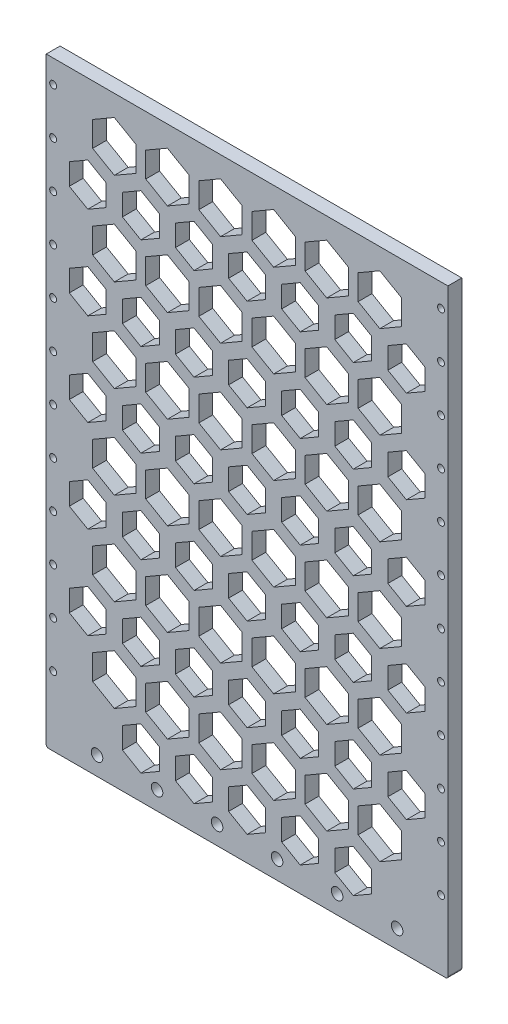
SolidWorks part; units mm, degrees
material "6061 Alloy"
ref_plane "前视基准面" through (0, 0, 0) normal (0, 0, 1) x (1, 0, 0)
ref_plane "上视基准面" through (0, 0, 0) normal (0, 1, 0) x (1, 0, 0)
ref_plane "右视基准面" through (0, 0, 0) normal (1, 0, 0) x (0, 0, -1)
sketch "Sketch1" plane through (0, 0, 0) normal (0, 0, 1) x (1, 0, 0)
  line L1 (-87, 90) -> (87, 90)
  line L2 (-87, 90) -> (-87, -150)
  line L3 (-87, -150) -> (87, -150)
  line L4 (87, 90) -> (87, -150)
  line L5 (-87, 90) -> (87, -150) construction
  line L6 (-87, -150) -> (87, 90) construction
  point P0 (0, -30)
  dimension "D1" = 174
  dimension "D2" = 240
extrude "Boss-Extrude1" add sketch "Sketch1" along normal blind 6
sketch "Sketch3" plane through (0, 0, 6) normal (0, 0, 1) x (1, 0, 0)
  line L6 (-77, -134) -> (77, -134) construction
  line L7 (-77, -134) -> (-77, -150) construction
  line L8 (-77, -150) -> (77, -150) construction
  line L9 (77, -134) -> (77, -150) construction
  line L10 (-77, -134) -> (77, -150) construction
  line L11 (-77, -150) -> (77, -134) construction
  circle A0 centre (-65, -142) radius 2.5
  circle A1 centre (-39, -142) radius 2.5
  circle A2 centre (-13, -142) radius 2.5
  circle A3 centre (13, -142) radius 2.5
  circle A4 centre (39, -142) radius 2.5
  circle A5 centre (65, -142) radius 2.5
  point P0 (0, -142)
  dimension "D1" = 12
  dimension "D2" = 6
extrude "Cut-Extrude1" cut sketch "Sketch3" against normal blind 6 contours A0 | A1 | A2 | A3 | A4 | A5
sketch "Sketch4" plane through (0, 90, 0) normal (0, 1, 0) x (1, 0, 0)
  line L4 (87, 0) -> (-87, 0)
  line L5 (-87, 0) -> (-87, -6)
  line L6 (-87, -6) -> (87, -6)
  line L7 (87, -6) -> (87, 0)
  line L8 (87, 0) -> (-87, 0)
  line L9 (-87, 0) -> (-87, -6)
  line L10 (-87, -6) -> (87, -6)
  line L11 (87, -6) -> (87, 0)
  dimension "D1" = 0
extrude "Boss-Extrude2" add sketch "Sketch4" along normal blind 20
sketch "Sketch6" plane through (0, 0, 6) normal (0, 0, 1) x (1, 0, 0)
  line L0 (-87, 110) -> (87, 110) construction
  line L2 (-87, 110) -> (-87, -150) construction
  line L3 (87, -150) -> (87, 110) construction
  circle A0 centre (-84, 100) radius 1.5
  circle A1 centre (-84, 80) radius 1.5
  circle A2 centre (-84, 60) radius 1.5
  circle A3 centre (-84, 40) radius 1.5
  circle A4 centre (-84, 20) radius 1.5
  circle A5 centre (-84, 0) radius 1.5
  circle A6 centre (-84, -20) radius 1.5
  circle A7 centre (-84, -40) radius 1.5
  circle A8 centre (-84, -60) radius 1.5
  circle A9 centre (-84, -80) radius 1.5
  circle A10 centre (-84, -100) radius 1.5
  circle A11 centre (-84, -120) radius 1.5
  circle A15 centre (84, 100) radius 1.5
  circle A16 centre (84, 80) radius 1.5
  circle A17 centre (84, 60) radius 1.5
  circle A18 centre (84, 40) radius 1.5
  circle A19 centre (84, 20) radius 1.5
  circle A20 centre (84, 0) radius 1.5
  circle A21 centre (84, -20) radius 1.5
  circle A22 centre (84, -40) radius 1.5
  circle A23 centre (84, -60) radius 1.5
  circle A24 centre (84, -80) radius 1.5
  circle A25 centre (84, -100) radius 1.5
  circle A26 centre (84, -120) radius 1.5
  circle A30 centre (-84, -160) radius 1.5 [skipped]
  circle A31 centre (-84, -180) radius 1.5 [skipped]
  circle A32 centre (84, -160) radius 1.5 [skipped]
  circle A33 centre (84, -180) radius 1.5 [skipped]
  circle A34 centre (-84, -140) radius 1.5 [skipped]
  circle A35 centre (84, -140) radius 1.5 [skipped]
  dimension "D3" = 15
  dimension "D5" = 3
  dimension "D1" = 10
  dimension "D2" = 3
  dimension "D4" = 3
  dimension "D6" = 10
  dimension "D7" = 15
extrude "Cut-Extrude2" cut sketch "Sketch6" against normal blind 10
sketch "Sketch7" plane through (0, 0, 6) normal (0, 0, 1) x (1, 0, 0)
  line L80 (-46, 60.7624) -> (-38, 65.3812)
  line L81 (-38, 65.3812) -> (-38, 74.6188)
  line L82 (-38, 74.6188) -> (-46, 79.2376)
  line L83 (-46, 79.2376) -> (-54, 74.6188)
  line L84 (-54, 74.6188) -> (-54, 65.3812)
  line L85 (-54, 65.3812) -> (-46, 60.7624)
  line L86 (-23, 60.7624) -> (-15, 65.3812)
  line L87 (-15, 65.3812) -> (-15, 74.6188)
  line L88 (-15, 74.6188) -> (-23, 79.2376)
  line L89 (-23, 79.2376) -> (-31, 74.6188)
  line L90 (-31, 74.6188) -> (-31, 65.3812)
  line L91 (-31, 65.3812) -> (-23, 60.7624)
  line L92 (0, 60.7624) -> (8, 65.3812)
  line L93 (8, 65.3812) -> (8, 74.6188)
  line L94 (8, 74.6188) -> (0, 79.2376)
  line L95 (0, 79.2376) -> (-8, 74.6188)
  line L96 (-8, 74.6188) -> (-8, 65.3812)
  line L97 (-8, 65.3812) -> (0, 60.7624)
  line L98 (23, 60.7624) -> (31, 65.3812)
  line L99 (31, 65.3812) -> (31, 74.6188)
  line L100 (31, 74.6188) -> (23, 79.2376)
  line L101 (23, 79.2376) -> (15, 74.6188)
  line L102 (15, 74.6188) -> (15, 65.3812)
  line L103 (15, 65.3812) -> (23, 60.7624)
  line L104 (46, 60.7624) -> (54, 65.3812)
  line L105 (54, 65.3812) -> (54, 74.6188)
  line L106 (54, 74.6188) -> (46, 79.2376)
  line L107 (46, 79.2376) -> (38, 74.6188)
  line L108 (38, 74.6188) -> (38, 65.3812)
  line L109 (38, 65.3812) -> (46, 60.7624)
  line L110 (69, 60.7624) -> (77, 65.3812)
  line L111 (77, 65.3812) -> (77, 74.6188)
  line L112 (77, 74.6188) -> (69, 79.2376)
  line L113 (69, 79.2376) -> (61, 74.6188)
  line L114 (61, 74.6188) -> (61, 65.3812)
  line L115 (61, 65.3812) -> (69, 60.7624)
  line L116 (-46, 20.7624) -> (-38, 25.3812)
  line L117 (-38, 25.3812) -> (-38, 34.6188)
  line L118 (-38, 34.6188) -> (-46, 39.2376)
  line L119 (-46, 39.2376) -> (-54, 34.6188)
  line L120 (-54, 34.6188) -> (-54, 25.3812)
  line L121 (-54, 25.3812) -> (-46, 20.7624)
  line L122 (-23, 20.7624) -> (-15, 25.3812)
  line L123 (-15, 25.3812) -> (-15, 34.6188)
  line L124 (-15, 34.6188) -> (-23, 39.2376)
  line L125 (-23, 39.2376) -> (-31, 34.6188)
  line L126 (-31, 34.6188) -> (-31, 25.3812)
  line L127 (-31, 25.3812) -> (-23, 20.7624)
  line L128 (0, 20.7624) -> (8, 25.3812)
  line L129 (8, 25.3812) -> (8, 34.6188)
  line L130 (8, 34.6188) -> (0, 39.2376)
  line L131 (0, 39.2376) -> (-8, 34.6188)
  line L132 (-8, 34.6188) -> (-8, 25.3812)
  line L133 (-8, 25.3812) -> (0, 20.7624)
  line L134 (23, 20.7624) -> (31, 25.3812)
  line L135 (31, 25.3812) -> (31, 34.6188)
  line L136 (31, 34.6188) -> (23, 39.2376)
  line L137 (23, 39.2376) -> (15, 34.6188)
  line L138 (15, 34.6188) -> (15, 25.3812)
  line L139 (15, 25.3812) -> (23, 20.7624)
  line L140 (46, 20.7624) -> (54, 25.3812)
  line L141 (54, 25.3812) -> (54, 34.6188)
  line L142 (54, 34.6188) -> (46, 39.2376)
  line L143 (46, 39.2376) -> (38, 34.6188)
  line L144 (38, 34.6188) -> (38, 25.3812)
  line L145 (38, 25.3812) -> (46, 20.7624)
  line L146 (69, 20.7624) -> (77, 25.3812)
  line L147 (77, 25.3812) -> (77, 34.6188)
  line L148 (77, 34.6188) -> (69, 39.2376)
  line L149 (69, 39.2376) -> (61, 34.6188)
  line L150 (61, 34.6188) -> (61, 25.3812)
  line L151 (61, 25.3812) -> (69, 20.7624)
  line L152 (-46, -19.2376) -> (-38, -14.6188)
  line L153 (-38, -14.6188) -> (-38, -5.3812)
  line L154 (-38, -5.3812) -> (-46, -0.7624)
  line L155 (-46, -0.7624) -> (-54, -5.3812)
  line L156 (-54, -5.3812) -> (-54, -14.6188)
  line L157 (-54, -14.6188) -> (-46, -19.2376)
  line L158 (-23, -19.2376) -> (-15, -14.6188)
  line L159 (-15, -14.6188) -> (-15, -5.3812)
  line L160 (-15, -5.3812) -> (-23, -0.7624)
  line L161 (-23, -0.7624) -> (-31, -5.3812)
  line L162 (-31, -5.3812) -> (-31, -14.6188)
  line L163 (-31, -14.6188) -> (-23, -19.2376)
  line L164 (0, -19.2376) -> (8, -14.6188)
  line L165 (8, -14.6188) -> (8, -5.3812)
  line L166 (8, -5.3812) -> (0, -0.7624)
  line L167 (0, -0.7624) -> (-8, -5.3812)
  line L168 (-8, -5.3812) -> (-8, -14.6188)
  line L169 (-8, -14.6188) -> (0, -19.2376)
  line L170 (23, -19.2376) -> (31, -14.6188)
  line L171 (31, -14.6188) -> (31, -5.3812)
  line L172 (31, -5.3812) -> (23, -0.7624)
  line L173 (23, -0.7624) -> (15, -5.3812)
  line L174 (15, -5.3812) -> (15, -14.6188)
  line L175 (15, -14.6188) -> (23, -19.2376)
  line L176 (46, -19.2376) -> (54, -14.6188)
  line L177 (54, -14.6188) -> (54, -5.3812)
  line L178 (54, -5.3812) -> (46, -0.7624)
  line L179 (46, -0.7624) -> (38, -5.3812)
  line L180 (38, -5.3812) -> (38, -14.6188)
  line L181 (38, -14.6188) -> (46, -19.2376)
  line L182 (69, -19.2376) -> (77, -14.6188)
  line L183 (77, -14.6188) -> (77, -5.3812)
  line L184 (77, -5.3812) -> (69, -0.7624)
  line L185 (69, -0.7624) -> (61, -5.3812)
  line L186 (61, -5.3812) -> (61, -14.6188)
  line L187 (61, -14.6188) -> (69, -19.2376)
  line L188 (-46, -59.2376) -> (-38, -54.6188)
  line L189 (-38, -54.6188) -> (-38, -45.3812)
  line L190 (-38, -45.3812) -> (-46, -40.7624)
  line L191 (-46, -40.7624) -> (-54, -45.3812)
  line L192 (-54, -45.3812) -> (-54, -54.6188)
  line L193 (-54, -54.6188) -> (-46, -59.2376)
  line L194 (-23, -59.2376) -> (-15, -54.6188)
  line L195 (-15, -54.6188) -> (-15, -45.3812)
  line L196 (-15, -45.3812) -> (-23, -40.7624)
  line L197 (-23, -40.7624) -> (-31, -45.3812)
  line L198 (-31, -45.3812) -> (-31, -54.6188)
  line L199 (-31, -54.6188) -> (-23, -59.2376)
  line L200 (0, -59.2376) -> (8, -54.6188)
  line L201 (8, -54.6188) -> (8, -45.3812)
  line L202 (8, -45.3812) -> (0, -40.7624)
  line L203 (0, -40.7624) -> (-8, -45.3812)
  line L204 (-8, -45.3812) -> (-8, -54.6188)
  line L205 (-8, -54.6188) -> (0, -59.2376)
  line L206 (23, -59.2376) -> (31, -54.6188)
  line L207 (31, -54.6188) -> (31, -45.3812)
  line L208 (31, -45.3812) -> (23, -40.7624)
  line L209 (23, -40.7624) -> (15, -45.3812)
  line L210 (15, -45.3812) -> (15, -54.6188)
  line L211 (15, -54.6188) -> (23, -59.2376)
  line L212 (46, -59.2376) -> (54, -54.6188)
  line L213 (54, -54.6188) -> (54, -45.3812)
  line L214 (54, -45.3812) -> (46, -40.7624)
  line L215 (46, -40.7624) -> (38, -45.3812)
  line L216 (38, -45.3812) -> (38, -54.6188)
  line L217 (38, -54.6188) -> (46, -59.2376)
  line L218 (69, -59.2376) -> (77, -54.6188)
  line L219 (77, -54.6188) -> (77, -45.3812)
  line L220 (77, -45.3812) -> (69, -40.7624)
  line L221 (69, -40.7624) -> (61, -45.3812)
  line L222 (61, -45.3812) -> (61, -54.6188)
  line L223 (61, -54.6188) -> (69, -59.2376)
  line L224 (-46, -99.2376) -> (-38, -94.6188)
  line L225 (-38, -94.6188) -> (-38, -85.3812)
  line L226 (-38, -85.3812) -> (-46, -80.7624)
  line L227 (-46, -80.7624) -> (-54, -85.3812)
  line L228 (-54, -85.3812) -> (-54, -94.6188)
  line L229 (-54, -94.6188) -> (-46, -99.2376)
  line L230 (-23, -99.2376) -> (-15, -94.6188)
  line L231 (-15, -94.6188) -> (-15, -85.3812)
  line L232 (-15, -85.3812) -> (-23, -80.7624)
  line L233 (-23, -80.7624) -> (-31, -85.3812)
  line L234 (-31, -85.3812) -> (-31, -94.6188)
  line L235 (-31, -94.6188) -> (-23, -99.2376)
  line L236 (0, -99.2376) -> (8, -94.6188)
  line L237 (8, -94.6188) -> (8, -85.3812)
  line L238 (8, -85.3812) -> (0, -80.7624)
  line L239 (0, -80.7624) -> (-8, -85.3812)
  line L240 (-8, -85.3812) -> (-8, -94.6188)
  line L241 (-8, -94.6188) -> (0, -99.2376)
  line L242 (23, -99.2376) -> (31, -94.6188)
  line L243 (31, -94.6188) -> (31, -85.3812)
  line L244 (31, -85.3812) -> (23, -80.7624)
  line L245 (23, -80.7624) -> (15, -85.3812)
  line L246 (15, -85.3812) -> (15, -94.6188)
  line L247 (15, -94.6188) -> (23, -99.2376)
  line L248 (46, -99.2376) -> (54, -94.6188)
  line L249 (54, -94.6188) -> (54, -85.3812)
  line L250 (54, -85.3812) -> (46, -80.7624)
  line L251 (46, -80.7624) -> (38, -85.3812)
  line L252 (38, -85.3812) -> (38, -94.6188)
  line L253 (38, -94.6188) -> (46, -99.2376)
  line L254 (69, -99.2376) -> (77, -94.6188)
  line L255 (77, -94.6188) -> (77, -85.3812)
  line L256 (77, -85.3812) -> (69, -80.7624)
  line L257 (69, -80.7624) -> (61, -85.3812)
  line L258 (61, -85.3812) -> (61, -94.6188)
  line L259 (61, -94.6188) -> (69, -99.2376)
  line L260 (-46, -139.2376) -> (-38, -134.6188)
  line L261 (-38, -134.6188) -> (-38, -125.3812)
  line L262 (-38, -125.3812) -> (-46, -120.7624)
  line L263 (-46, -120.7624) -> (-54, -125.3812)
  line L264 (-54, -125.3812) -> (-54, -134.6188)
  line L265 (-54, -134.6188) -> (-46, -139.2376)
  line L266 (-23, -139.2376) -> (-15, -134.6188)
  line L267 (-15, -134.6188) -> (-15, -125.3812)
  line L268 (-15, -125.3812) -> (-23, -120.7624)
  line L269 (-23, -120.7624) -> (-31, -125.3812)
  line L270 (-31, -125.3812) -> (-31, -134.6188)
  line L271 (-31, -134.6188) -> (-23, -139.2376)
  line L272 (0, -139.2376) -> (8, -134.6188)
  line L273 (8, -134.6188) -> (8, -125.3812)
  line L274 (8, -125.3812) -> (0, -120.7624)
  line L275 (0, -120.7624) -> (-8, -125.3812)
  line L276 (-8, -125.3812) -> (-8, -134.6188)
  line L277 (-8, -134.6188) -> (0, -139.2376)
  line L278 (23, -139.2376) -> (31, -134.6188)
  line L279 (31, -134.6188) -> (31, -125.3812)
  line L280 (31, -125.3812) -> (23, -120.7624)
  line L281 (23, -120.7624) -> (15, -125.3812)
  line L282 (15, -125.3812) -> (15, -134.6188)
  line L283 (15, -134.6188) -> (23, -139.2376)
  line L284 (46, -139.2376) -> (54, -134.6188)
  line L285 (54, -134.6188) -> (54, -125.3812)
  line L286 (54, -125.3812) -> (46, -120.7624)
  line L287 (46, -120.7624) -> (38, -125.3812)
  line L288 (38, -125.3812) -> (38, -134.6188)
  line L289 (38, -134.6188) -> (46, -139.2376)
  line L302 (-69, 60.7624) -> (-61, 65.3812)
  line L303 (-61, 65.3812) -> (-61, 74.6188)
  line L304 (-61, 74.6188) -> (-69, 79.2376)
  line L305 (-69, 79.2376) -> (-77, 74.6188)
  line L306 (-77, 74.6188) -> (-77, 65.3812)
  line L307 (-77, 65.3812) -> (-69, 60.7624)
  line L308 (-69, 20.7624) -> (-61, 25.3812)
  line L309 (-61, 25.3812) -> (-61, 34.6188)
  line L310 (-61, 34.6188) -> (-69, 39.2376)
  line L311 (-69, 39.2376) -> (-77, 34.6188)
  line L312 (-77, 34.6188) -> (-77, 25.3812)
  line L313 (-77, 25.3812) -> (-69, 20.7624)
  line L314 (-69, -19.2376) -> (-61, -14.6188)
  line L315 (-61, -14.6188) -> (-61, -5.3812)
  line L316 (-61, -5.3812) -> (-69, -0.7624)
  line L317 (-69, -0.7624) -> (-77, -5.3812)
  line L318 (-77, -5.3812) -> (-77, -14.6188)
  line L319 (-77, -14.6188) -> (-69, -19.2376)
  line L320 (-69, -59.2376) -> (-61, -54.6188)
  line L321 (-61, -54.6188) -> (-61, -45.3812)
  line L322 (-61, -45.3812) -> (-69, -40.7624)
  line L323 (-69, -40.7624) -> (-77, -45.3812)
  line L324 (-77, -45.3812) -> (-77, -54.6188)
  line L325 (-77, -54.6188) -> (-69, -59.2376)
  line L326 (-69, -99.2376) -> (-61, -94.6188)
  line L327 (-61, -94.6188) -> (-61, -85.3812)
  line L328 (-61, -85.3812) -> (-69, -80.7624)
  line L329 (-69, -80.7624) -> (-77, -85.3812)
  line L330 (-77, -85.3812) -> (-77, -94.6188)
  line L331 (-77, -94.6188) -> (-69, -99.2376)
  line L376 (-34.5, 79.2376) -> (-25.109, 84.6595)
  line L377 (-25.109, 84.6595) -> (-25.109, 95.5033)
  line L378 (-25.109, 95.5033) -> (-34.5, 100.9252)
  line L379 (-34.5, 100.9252) -> (-43.891, 95.5033)
  line L380 (-43.891, 95.5033) -> (-43.891, 84.6595)
  line L381 (-43.891, 84.6595) -> (-34.5, 79.2376)
  line L382 (-11.5, 79.2376) -> (-2.109, 84.6595)
  line L383 (-2.109, 84.6595) -> (-2.109, 95.5033)
  line L384 (-2.109, 95.5033) -> (-11.5, 100.9252)
  line L385 (-11.5, 100.9252) -> (-20.891, 95.5033)
  line L386 (-20.891, 95.5033) -> (-20.891, 84.6595)
  line L387 (-20.891, 84.6595) -> (-11.5, 79.2376)
  line L388 (11.5, 79.2376) -> (20.891, 84.6595)
  line L389 (20.891, 84.6595) -> (20.891, 95.5033)
  line L390 (20.891, 95.5033) -> (11.5, 100.9252)
  line L391 (11.5, 100.9252) -> (2.109, 95.5033)
  line L392 (2.109, 95.5033) -> (2.109, 84.6595)
  line L393 (2.109, 84.6595) -> (11.5, 79.2376)
  line L394 (34.5, 79.2376) -> (43.891, 84.6595)
  line L395 (43.891, 84.6595) -> (43.891, 95.5033)
  line L396 (43.891, 95.5033) -> (34.5, 100.9252)
  line L397 (34.5, 100.9252) -> (25.109, 95.5033)
  line L398 (25.109, 95.5033) -> (25.109, 84.6595)
  line L399 (25.109, 84.6595) -> (34.5, 79.2376)
  line L400 (57.5, 79.2376) -> (66.891, 84.6595)
  line L401 (66.891, 84.6595) -> (66.891, 95.5033)
  line L402 (66.891, 95.5033) -> (57.5, 100.9252)
  line L403 (57.5, 100.9252) -> (48.109, 95.5033)
  line L404 (48.109, 95.5033) -> (48.109, 84.6595)
  line L405 (48.109, 84.6595) -> (57.5, 79.2376)
  line L406 (-34.5, 39.2376) -> (-25.109, 44.6595)
  line L407 (-25.109, 44.6595) -> (-25.109, 55.5033)
  line L408 (-25.109, 55.5033) -> (-34.5, 60.9252)
  line L409 (-34.5, 60.9252) -> (-43.891, 55.5033)
  line L410 (-43.891, 55.5033) -> (-43.891, 44.6595)
  line L411 (-43.891, 44.6595) -> (-34.5, 39.2376)
  line L412 (-11.5, 39.2376) -> (-2.109, 44.6595)
  line L413 (-2.109, 44.6595) -> (-2.109, 55.5033)
  line L414 (-2.109, 55.5033) -> (-11.5, 60.9252)
  line L415 (-11.5, 60.9252) -> (-20.891, 55.5033)
  line L416 (-20.891, 55.5033) -> (-20.891, 44.6595)
  line L417 (-20.891, 44.6595) -> (-11.5, 39.2376)
  line L418 (11.5, 39.2376) -> (20.891, 44.6595)
  line L419 (20.891, 44.6595) -> (20.891, 55.5033)
  line L420 (20.891, 55.5033) -> (11.5, 60.9252)
  line L421 (11.5, 60.9252) -> (2.109, 55.5033)
  line L422 (2.109, 55.5033) -> (2.109, 44.6595)
  line L423 (2.109, 44.6595) -> (11.5, 39.2376)
  line L424 (34.5, 39.2376) -> (43.891, 44.6595)
  line L425 (43.891, 44.6595) -> (43.891, 55.5033)
  line L426 (43.891, 55.5033) -> (34.5, 60.9252)
  line L427 (34.5, 60.9252) -> (25.109, 55.5033)
  line L428 (25.109, 55.5033) -> (25.109, 44.6595)
  line L429 (25.109, 44.6595) -> (34.5, 39.2376)
  line L430 (57.5, 39.2376) -> (66.891, 44.6595)
  line L431 (66.891, 44.6595) -> (66.891, 55.5033)
  line L432 (66.891, 55.5033) -> (57.5, 60.9252)
  line L433 (57.5, 60.9252) -> (48.109, 55.5033)
  line L434 (48.109, 55.5033) -> (48.109, 44.6595)
  line L435 (48.109, 44.6595) -> (57.5, 39.2376)
  line L436 (-34.5, -0.7624) -> (-25.109, 4.6595)
  line L437 (-25.109, 4.6595) -> (-25.109, 15.5033)
  line L438 (-25.109, 15.5033) -> (-34.5, 20.9252)
  line L439 (-34.5, 20.9252) -> (-43.891, 15.5033)
  line L440 (-43.891, 15.5033) -> (-43.891, 4.6595)
  line L441 (-43.891, 4.6595) -> (-34.5, -0.7624)
  line L442 (-11.5, -0.7624) -> (-2.109, 4.6595)
  line L443 (-2.109, 4.6595) -> (-2.109, 15.5033)
  line L444 (-2.109, 15.5033) -> (-11.5, 20.9252)
  line L445 (-11.5, 20.9252) -> (-20.891, 15.5033)
  line L446 (-20.891, 15.5033) -> (-20.891, 4.6595)
  line L447 (-20.891, 4.6595) -> (-11.5, -0.7624)
  line L448 (11.5, -0.7624) -> (20.891, 4.6595)
  line L449 (20.891, 4.6595) -> (20.891, 15.5033)
  line L450 (20.891, 15.5033) -> (11.5, 20.9252)
  line L451 (11.5, 20.9252) -> (2.109, 15.5033)
  line L452 (2.109, 15.5033) -> (2.109, 4.6595)
  line L453 (2.109, 4.6595) -> (11.5, -0.7624)
  line L454 (34.5, -0.7624) -> (43.891, 4.6595)
  line L455 (43.891, 4.6595) -> (43.891, 15.5033)
  line L456 (43.891, 15.5033) -> (34.5, 20.9252)
  line L457 (34.5, 20.9252) -> (25.109, 15.5033)
  line L458 (25.109, 15.5033) -> (25.109, 4.6595)
  line L459 (25.109, 4.6595) -> (34.5, -0.7624)
  line L460 (57.5, -0.7624) -> (66.891, 4.6595)
  line L461 (66.891, 4.6595) -> (66.891, 15.5033)
  line L462 (66.891, 15.5033) -> (57.5, 20.9252)
  line L463 (57.5, 20.9252) -> (48.109, 15.5033)
  line L464 (48.109, 15.5033) -> (48.109, 4.6595)
  line L465 (48.109, 4.6595) -> (57.5, -0.7624)
  line L466 (-34.5, -40.7624) -> (-25.109, -35.3405)
  line L467 (-25.109, -35.3405) -> (-25.109, -24.4967)
  line L468 (-25.109, -24.4967) -> (-34.5, -19.0748)
  line L469 (-34.5, -19.0748) -> (-43.891, -24.4967)
  line L470 (-43.891, -24.4967) -> (-43.891, -35.3405)
  line L471 (-43.891, -35.3405) -> (-34.5, -40.7624)
  line L472 (-11.5, -40.7624) -> (-2.109, -35.3405)
  line L473 (-2.109, -35.3405) -> (-2.109, -24.4967)
  line L474 (-2.109, -24.4967) -> (-11.5, -19.0748)
  line L475 (-11.5, -19.0748) -> (-20.891, -24.4967)
  line L476 (-20.891, -24.4967) -> (-20.891, -35.3405)
  line L477 (-20.891, -35.3405) -> (-11.5, -40.7624)
  line L478 (11.5, -40.7624) -> (20.891, -35.3405)
  line L479 (20.891, -35.3405) -> (20.891, -24.4967)
  line L480 (20.891, -24.4967) -> (11.5, -19.0748)
  line L481 (11.5, -19.0748) -> (2.109, -24.4967)
  line L482 (2.109, -24.4967) -> (2.109, -35.3405)
  line L483 (2.109, -35.3405) -> (11.5, -40.7624)
  line L484 (34.5, -40.7624) -> (43.891, -35.3405)
  line L485 (43.891, -35.3405) -> (43.891, -24.4967)
  line L486 (43.891, -24.4967) -> (34.5, -19.0748)
  line L487 (34.5, -19.0748) -> (25.109, -24.4967)
  line L488 (25.109, -24.4967) -> (25.109, -35.3405)
  line L489 (25.109, -35.3405) -> (34.5, -40.7624)
  line L490 (57.5, -40.7624) -> (66.891, -35.3405)
  line L491 (66.891, -35.3405) -> (66.891, -24.4967)
  line L492 (66.891, -24.4967) -> (57.5, -19.0748)
  line L493 (57.5, -19.0748) -> (48.109, -24.4967)
  line L494 (48.109, -24.4967) -> (48.109, -35.3405)
  line L495 (48.109, -35.3405) -> (57.5, -40.7624)
  line L496 (-34.5, -80.7624) -> (-25.109, -75.3405)
  line L497 (-25.109, -75.3405) -> (-25.109, -64.4967)
  line L498 (-25.109, -64.4967) -> (-34.5, -59.0748)
  line L499 (-34.5, -59.0748) -> (-43.891, -64.4967)
  line L500 (-43.891, -64.4967) -> (-43.891, -75.3405)
  line L501 (-43.891, -75.3405) -> (-34.5, -80.7624)
  line L502 (-11.5, -80.7624) -> (-2.109, -75.3405)
  line L503 (-2.109, -75.3405) -> (-2.109, -64.4967)
  line L504 (-2.109, -64.4967) -> (-11.5, -59.0748)
  line L505 (-11.5, -59.0748) -> (-20.891, -64.4967)
  line L506 (-20.891, -64.4967) -> (-20.891, -75.3405)
  line L507 (-20.891, -75.3405) -> (-11.5, -80.7624)
  line L508 (11.5, -80.7624) -> (20.891, -75.3405)
  line L509 (20.891, -75.3405) -> (20.891, -64.4967)
  line L510 (20.891, -64.4967) -> (11.5, -59.0748)
  line L511 (11.5, -59.0748) -> (2.109, -64.4967)
  line L512 (2.109, -64.4967) -> (2.109, -75.3405)
  line L513 (2.109, -75.3405) -> (11.5, -80.7624)
  line L514 (34.5, -80.7624) -> (43.891, -75.3405)
  line L515 (43.891, -75.3405) -> (43.891, -64.4967)
  line L516 (43.891, -64.4967) -> (34.5, -59.0748)
  line L517 (34.5, -59.0748) -> (25.109, -64.4967)
  line L518 (25.109, -64.4967) -> (25.109, -75.3405)
  line L519 (25.109, -75.3405) -> (34.5, -80.7624)
  line L520 (57.5, -80.7624) -> (66.891, -75.3405)
  line L521 (66.891, -75.3405) -> (66.891, -64.4967)
  line L522 (66.891, -64.4967) -> (57.5, -59.0748)
  line L523 (57.5, -59.0748) -> (48.109, -64.4967)
  line L524 (48.109, -64.4967) -> (48.109, -75.3405)
  line L525 (48.109, -75.3405) -> (57.5, -80.7624)
  line L526 (-34.5, -120.7624) -> (-25.109, -115.3405)
  line L527 (-25.109, -115.3405) -> (-25.109, -104.4967)
  line L528 (-25.109, -104.4967) -> (-34.5, -99.0748)
  line L529 (-34.5, -99.0748) -> (-43.891, -104.4967)
  line L530 (-43.891, -104.4967) -> (-43.891, -115.3405)
  line L531 (-43.891, -115.3405) -> (-34.5, -120.7624)
  line L532 (-11.5, -120.7624) -> (-2.109, -115.3405)
  line L533 (-2.109, -115.3405) -> (-2.109, -104.4967)
  line L534 (-2.109, -104.4967) -> (-11.5, -99.0748)
  line L535 (-11.5, -99.0748) -> (-20.891, -104.4967)
  line L536 (-20.891, -104.4967) -> (-20.891, -115.3405)
  line L537 (-20.891, -115.3405) -> (-11.5, -120.7624)
  line L538 (11.5, -120.7624) -> (20.891, -115.3405)
  line L539 (20.891, -115.3405) -> (20.891, -104.4967)
  line L540 (20.891, -104.4967) -> (11.5, -99.0748)
  line L541 (11.5, -99.0748) -> (2.109, -104.4967)
  line L542 (2.109, -104.4967) -> (2.109, -115.3405)
  line L543 (2.109, -115.3405) -> (11.5, -120.7624)
  line L544 (34.5, -120.7624) -> (43.891, -115.3405)
  line L545 (43.891, -115.3405) -> (43.891, -104.4967)
  line L546 (43.891, -104.4967) -> (34.5, -99.0748)
  line L547 (34.5, -99.0748) -> (25.109, -104.4967)
  line L548 (25.109, -104.4967) -> (25.109, -115.3405)
  line L549 (25.109, -115.3405) -> (34.5, -120.7624)
  line L550 (57.5, -120.7624) -> (66.891, -115.3405)
  line L551 (66.891, -115.3405) -> (66.891, -104.4967)
  line L552 (66.891, -104.4967) -> (57.5, -99.0748)
  line L553 (57.5, -99.0748) -> (48.109, -104.4967)
  line L554 (48.109, -104.4967) -> (48.109, -115.3405)
  line L555 (48.109, -115.3405) -> (57.5, -120.7624)
  line L556 (-57.5, 79.2376) -> (-48.109, 84.6595)
  line L557 (-48.109, 84.6595) -> (-48.109, 95.5033)
  line L558 (-48.109, 95.5033) -> (-57.5, 100.9252)
  line L559 (-57.5, 100.9252) -> (-66.891, 95.5033)
  line L560 (-66.891, 95.5033) -> (-66.891, 84.6595)
  line L561 (-66.891, 84.6595) -> (-57.5, 79.2376)
  line L562 (-57.5, 39.2376) -> (-48.109, 44.6595)
  line L563 (-48.109, 44.6595) -> (-48.109, 55.5033)
  line L564 (-48.109, 55.5033) -> (-57.5, 60.9252)
  line L565 (-57.5, 60.9252) -> (-66.891, 55.5033)
  line L566 (-66.891, 55.5033) -> (-66.891, 44.6595)
  line L567 (-66.891, 44.6595) -> (-57.5, 39.2376)
  line L568 (-57.5, -0.7624) -> (-48.109, 4.6595)
  line L569 (-48.109, 4.6595) -> (-48.109, 15.5033)
  line L570 (-48.109, 15.5033) -> (-57.5, 20.9252)
  line L571 (-57.5, 20.9252) -> (-66.891, 15.5033)
  line L572 (-66.891, 15.5033) -> (-66.891, 4.6595)
  line L573 (-66.891, 4.6595) -> (-57.5, -0.7624)
  line L574 (-57.5, -40.7624) -> (-48.109, -35.3405)
  line L575 (-48.109, -35.3405) -> (-48.109, -24.4967)
  line L576 (-48.109, -24.4967) -> (-57.5, -19.0748)
  line L577 (-57.5, -19.0748) -> (-66.891, -24.4967)
  line L578 (-66.891, -24.4967) -> (-66.891, -35.3405)
  line L579 (-66.891, -35.3405) -> (-57.5, -40.7624)
  line L580 (-57.5, -80.7624) -> (-48.109, -75.3405)
  line L581 (-48.109, -75.3405) -> (-48.109, -64.4967)
  line L582 (-48.109, -64.4967) -> (-57.5, -59.0748)
  line L583 (-57.5, -59.0748) -> (-66.891, -64.4967)
  line L584 (-66.891, -64.4967) -> (-66.891, -75.3405)
  line L585 (-66.891, -75.3405) -> (-57.5, -80.7624)
  line L586 (-57.5, -120.7624) -> (-48.109, -115.3405)
  line L587 (-48.109, -115.3405) -> (-48.109, -104.4967)
  line L588 (-48.109, -104.4967) -> (-57.5, -99.0748)
  line L589 (-57.5, -99.0748) -> (-66.891, -104.4967)
  line L590 (-66.891, -104.4967) -> (-66.891, -115.3405)
  line L591 (-66.891, -115.3405) -> (-57.5, -120.7624)
  circle A13 centre (-46, 70) radius 8 construction
  circle A14 centre (-23, 70) radius 8 construction
  circle A15 centre (0, 70) radius 8 construction
  circle A16 centre (23, 70) radius 8 construction
  circle A17 centre (46, 70) radius 8 construction
  circle A18 centre (69, 70) radius 8 construction
  circle A19 centre (-46, 30) radius 8 construction
  circle A20 centre (-23, 30) radius 8 construction
  circle A21 centre (0, 30) radius 8 construction
  circle A22 centre (23, 30) radius 8 construction
  circle A23 centre (46, 30) radius 8 construction
  circle A24 centre (69, 30) radius 8 construction
  circle A25 centre (-46, -10) radius 8 construction
  circle A26 centre (-23, -10) radius 8 construction
  circle A27 centre (0, -10) radius 8 construction
  circle A28 centre (23, -10) radius 8 construction
  circle A29 centre (46, -10) radius 8 construction
  circle A30 centre (69, -10) radius 8 construction
  circle A31 centre (-46, -50) radius 8 construction
  circle A32 centre (-23, -50) radius 8 construction
  circle A33 centre (0, -50) radius 8 construction
  circle A34 centre (23, -50) radius 8 construction
  circle A35 centre (46, -50) radius 8 construction
  circle A36 centre (69, -50) radius 8 construction
  circle A37 centre (-46, -90) radius 8 construction
  circle A38 centre (-23, -90) radius 8 construction
  circle A39 centre (0, -90) radius 8 construction
  circle A40 centre (23, -90) radius 8 construction
  circle A41 centre (46, -90) radius 8 construction
  circle A42 centre (69, -90) radius 8 construction
  circle A43 centre (-46, -130) radius 8 construction
  circle A44 centre (-23, -130) radius 8 construction
  circle A45 centre (0, -130) radius 8 construction
  circle A46 centre (23, -130) radius 8 construction
  circle A47 centre (46, -130) radius 8 construction
  circle A50 centre (-69, 70) radius 8 construction
  circle A51 centre (-69, 30) radius 8 construction
  circle A52 centre (-69, -10) radius 8 construction
  circle A53 centre (-69, -50) radius 8 construction
  circle A54 centre (-69, -90) radius 8 construction
extrude "Cut-Extrude3" cut sketch "Sketch7" against normal blind 10
fillet "Fillet2" radius 1 3 edges at (-87, -150, 3) (87, -150, 3) (0, -150, 0)
